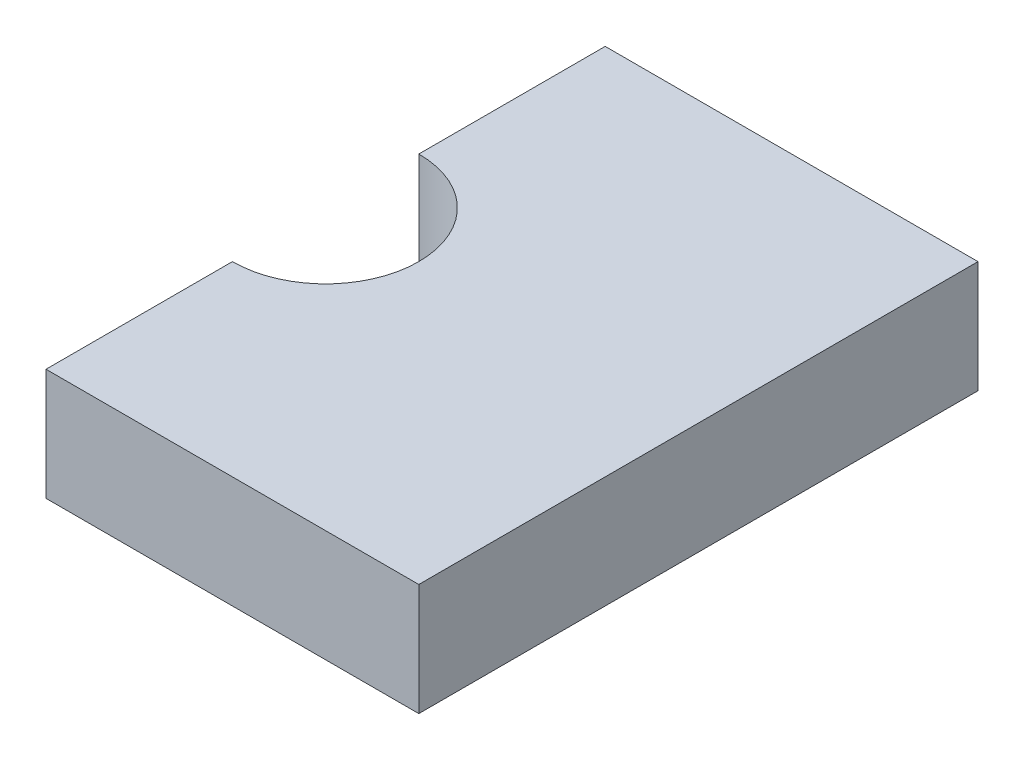
SolidWorks part; units mm, degrees
ref_plane "Спереди" through (0, 0, 0) normal (0, 0, 1) x (1, 0, 0)
ref_plane "Сверху" through (0, 0, 0) normal (0, 1, 0) x (1, 0, 0)
ref_plane "Справа" through (0, 0, 0) normal (1, 0, 0) x (0, 0, -1)
sketch "Эскиз1" plane through (0, 0, 0) normal (0, 1, 0) x (1, 0, 0)
  line L0 (0, 15) -> (0, 10)
  line L1 (0, 0) -> (10, 0)
  line L2 (0, 7.5) -> (0, 17.5) construction
  line L3 (0, 15) -> (10, 15)
  line L4 (10, 0) -> (10, 15)
  line L5 (0, 0) -> (0, 5)
  arc A0 (0, 10) -> (0, 5) centre (0, 7.5) cw
extrude "Бобышка-Вытянуть1" add sketch "Эскиз1" along normal blind 3
